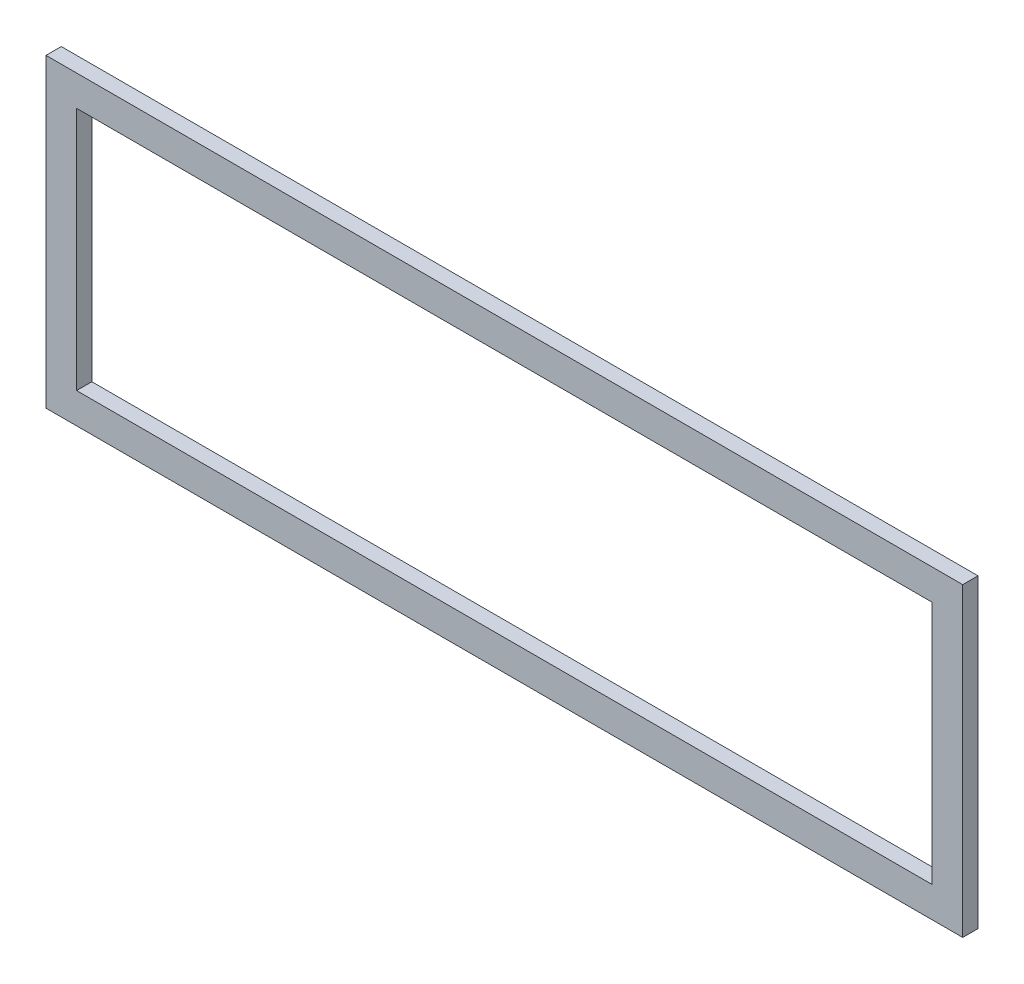
SolidWorks part; units mm, degrees
ref_plane "Front Plane" through (0, 0, 0) normal (0, 0, 1) x (1, 0, 0)
ref_plane "Top Plane" through (0, 0, 0) normal (0, 1, 0) x (1, 0, 0)
ref_plane "Right Plane" through (0, 0, 0) normal (1, 0, 0) x (0, 0, -1)
sketch "Sketch1" plane through (0, 0, 0) normal (0, 0, 1) x (1, 0, 0)
  line L1 (-150, -50) -> (150, -50)
  line L2 (-150, -50) -> (-150, 50)
  line L3 (-150, 50) -> (150, 50)
  line L4 (150, -50) -> (150, 50)
  line L5 (-150, -50) -> (150, 50) construction
  line L6 (-150, 50) -> (150, -50) construction
  line L7 (-140, -40) -> (140, -40)
  line L8 (-140, -40) -> (-140, 40)
  line L9 (-140, 40) -> (140, 40)
  line L10 (140, -40) -> (140, 40)
  line L11 (-140, -40) -> (140, 40) construction
  line L12 (-140, 40) -> (140, -40) construction
  point P0 (0, 0)
  point P6 (0, 0)
  dimension "D1" = 10
  dimension "D2" = 300
  dimension "D3" = 100
  dimension "D4" = 10
extrude "Boss-Extrude1" add sketch "Sketch1" along normal mid plane 5
